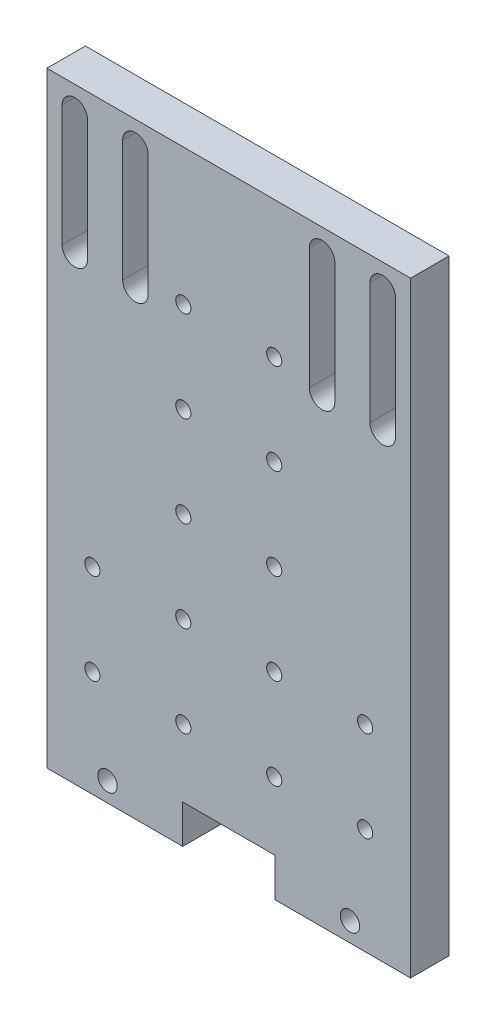
SolidWorks part; units mm, degrees
ref_plane "Front" through (0, 0, 0) normal (0, 0, 1) x (1, 0, 0)
ref_plane "Top" through (0, 0, 0) normal (0, 1, 0) x (1, 0, 0)
ref_plane "Right" through (0, 0, 0) normal (1, 0, 0) x (0, 0, -1)
ref_plane "Plane1" through (0, 0, 118.2886) normal (0, 0, 1) x (1, 0, 0)
sketch "Sketch1" plane through (0, 0, 118.2886) normal (0, 0, 1) x (1, 0, 0)
  line L0 (19.6347, 102.189) -> (19.6347, 2.189)
  line L1 (19.6347, 2.189) -> (42.0347, 2.189)
  line L2 (42.0347, 2.189) -> (42.0347, 8.539)
  line L3 (42.0347, 8.539) -> (57.2347, 8.539)
  line L4 (57.2347, 8.539) -> (57.2347, 2.189)
  line L5 (57.2347, 2.189) -> (79.6347, 2.189)
  line L6 (79.6347, 2.189) -> (79.6347, 102.189)
  line L7 (79.6347, 102.189) -> (19.6347, 102.189)
  dimension "D1" = 15.2
  dimension "D2" = 6.35
  dimension "D3" = 60
  dimension "D4" = 100
extrude "Boss-Extrude1" add sketch "Sketch1" against normal blind 6.35
hole_wizard "Ø2.5 (2.5) Diameter Hole1" positions "Sketch7" profile "Sketch6" hole size "Ø2.5" standard "ANSI Metric"
sketch "Sketch7" plane through (0, 0, 111.9386) normal (0, 0, -1) x (-1, 0, 0)
  point P0 (-27.1347, 19.689)
sketch "Sketch6" plane through (27.1347, 19.689, 111.9386) normal (1, 0, 0) x (0, 1, 0)
  line L0 (0, 0) -> (0, 6.35)
  line L1 (0, 6.35) -> (1.25, 6.35)
  line L2 (1.25, 6.35) -> (1.25, 0)
  line L5 (1.25, 0) -> (0, 0)
  line L11 (0, -6.35) -> (0, 107.95) construction
  dimension "Thru Hole Dia." = 2.5
  dimension "Thru Hole Depth" = 6.35
hole_wizard "Ø3.2 (3.2) Diameter Hole1" positions "Sketch9" profile "Sketch8" hole size "Ø3.2" standard "ANSI Metric"
sketch "Sketch9" plane through (0, 0, 118.2886) normal (0, 0, 1) x (1, 0, 0)
  point P0 (29.6347, 5.364)
sketch "Sketch8" plane through (29.6347, 5.364, 118.2886) normal (1, 0, 0) x (0, -1, 0)
  line L0 (0, 0) -> (0, 6.35)
  line L1 (0, 6.35) -> (1.6, 6.35)
  line L2 (1.6, 6.35) -> (1.6, 0)
  line L5 (1.6, 0) -> (0, 0)
  line L11 (0, -6.35) -> (0, 107.95) construction
  dimension "Thru Hole Dia." = 3.2
  dimension "Thru Hole Depth" = 6.35
hole_wizard "Ø2.5 (2.5) Diameter Hole2" positions "Sketch11" profile "Sketch10" hole size "Ø2.5" standard "ANSI Metric"
sketch "Sketch11" plane through (0, 0, 111.9386) normal (0, 0, -1) x (-1, 0, 0)
  point P0 (-57.1347, 19.689)
sketch "Sketch10" plane through (57.1347, 19.689, 111.9386) normal (1, 0, 0) x (0, 1, 0)
  line L0 (0, 0) -> (0, 6.35)
  line L1 (0, 6.35) -> (1.25, 6.35)
  line L2 (1.25, 6.35) -> (1.25, 0)
  line L5 (1.25, 0) -> (0, 0)
  line L11 (0, -6.35) -> (0, 107.95) construction
  dimension "Thru Hole Dia." = 2.5
  dimension "Thru Hole Depth" = 6.35
hole_wizard "Ø2.5 (2.5) Diameter Hole3" positions "Sketch13" profile "Sketch12" hole size "Ø2.5" standard "ANSI Metric"
sketch "Sketch13" plane through (0, 0, 111.9386) normal (0, 0, -1) x (-1, 0, 0)
  point P0 (-42.1347, 34.689)
sketch "Sketch12" plane through (42.1347, 34.689, 111.9386) normal (1, 0, 0) x (0, 1, 0)
  line L0 (0, 0) -> (0, 6.35)
  line L1 (0, 6.35) -> (1.25, 6.35)
  line L2 (1.25, 6.35) -> (1.25, 0)
  line L5 (1.25, 0) -> (0, 0)
  line L11 (0, -6.35) -> (0, 107.95) construction
  dimension "Thru Hole Dia." = 2.5
  dimension "Thru Hole Depth" = 6.35
hole_wizard "Ø2.5 (2.5) Diameter Hole4" positions "Sketch15" profile "Sketch14" hole size "Ø2.5" standard "ANSI Metric"
sketch "Sketch15" plane through (0, 0, 111.9386) normal (0, 0, -1) x (-1, 0, 0)
  point P0 (-42.1347, 64.689)
sketch "Sketch14" plane through (42.1347, 64.689, 111.9386) normal (1, 0, 0) x (0, 1, 0)
  line L0 (0, 0) -> (0, 6.35)
  line L1 (0, 6.35) -> (1.25, 6.35)
  line L2 (1.25, 6.35) -> (1.25, 0)
  line L5 (1.25, 0) -> (0, 0)
  line L11 (0, -6.35) -> (0, 107.95) construction
  dimension "Thru Hole Dia." = 2.5
  dimension "Thru Hole Depth" = 6.35
hole_wizard "Ø2.5 (2.5) Diameter Hole5" positions "Sketch17" profile "Sketch16" hole size "Ø2.5" standard "ANSI Metric"
sketch "Sketch17" plane through (0, 0, 111.9386) normal (0, 0, -1) x (-1, 0, 0)
  point P0 (-57.1347, 64.689)
sketch "Sketch16" plane through (57.1347, 64.689, 111.9386) normal (1, 0, 0) x (0, 1, 0)
  line L0 (0, 0) -> (0, 6.35)
  line L1 (0, 6.35) -> (1.25, 6.35)
  line L2 (1.25, 6.35) -> (1.25, 0)
  line L5 (1.25, 0) -> (0, 0)
  line L11 (0, -6.35) -> (0, 107.95) construction
  dimension "Thru Hole Dia." = 2.5
  dimension "Thru Hole Depth" = 6.35
hole_wizard "Ø2.5 (2.5) Diameter Hole6" positions "Sketch19" profile "Sketch18" hole size "Ø2.5" standard "ANSI Metric"
sketch "Sketch19" plane through (0, 0, 111.9386) normal (0, 0, -1) x (-1, 0, 0)
  point P0 (-27.1347, 34.689)
sketch "Sketch18" plane through (27.1347, 34.689, 111.9386) normal (1, 0, 0) x (0, 1, 0)
  line L0 (0, 0) -> (0, 6.35)
  line L1 (0, 6.35) -> (1.25, 6.35)
  line L2 (1.25, 6.35) -> (1.25, 0)
  line L5 (1.25, 0) -> (0, 0)
  line L11 (0, -6.35) -> (0, 107.95) construction
  dimension "Thru Hole Dia." = 2.5
  dimension "Thru Hole Depth" = 6.35
hole_wizard "Ø2.5 (2.5) Diameter Hole7" positions "Sketch21" profile "Sketch20" hole size "Ø2.5" standard "ANSI Metric"
sketch "Sketch21" plane through (0, 0, 111.9386) normal (0, 0, -1) x (-1, 0, 0)
  point P0 (-72.1347, 19.689)
sketch "Sketch20" plane through (72.1347, 19.689, 111.9386) normal (1, 0, 0) x (0, 1, 0)
  line L0 (0, 0) -> (0, 6.35)
  line L1 (0, 6.35) -> (1.25, 6.35)
  line L2 (1.25, 6.35) -> (1.25, 0)
  line L5 (1.25, 0) -> (0, 0)
  line L11 (0, -6.35) -> (0, 107.95) construction
  dimension "Thru Hole Dia." = 2.5
  dimension "Thru Hole Depth" = 6.35
hole_wizard "Ø2.5 (2.5) Diameter Hole8" positions "Sketch23" profile "Sketch22" hole size "Ø2.5" standard "ANSI Metric"
sketch "Sketch23" plane through (0, 0, 111.9386) normal (0, 0, -1) x (-1, 0, 0)
  point P0 (-42.1347, 19.689)
sketch "Sketch22" plane through (42.1347, 19.689, 111.9386) normal (1, 0, 0) x (0, 1, 0)
  line L0 (0, 0) -> (0, 6.35)
  line L1 (0, 6.35) -> (1.25, 6.35)
  line L2 (1.25, 6.35) -> (1.25, 0)
  line L5 (1.25, 0) -> (0, 0)
  line L11 (0, -6.35) -> (0, 107.95) construction
  dimension "Thru Hole Dia." = 2.5
  dimension "Thru Hole Depth" = 6.35
hole_wizard "Ø2.5 (2.5) Diameter Hole9" positions "Sketch25" profile "Sketch24" hole size "Ø2.5" standard "ANSI Metric"
sketch "Sketch25" plane through (0, 0, 111.9386) normal (0, 0, -1) x (-1, 0, 0)
  point P0 (-57.1347, 34.689)
sketch "Sketch24" plane through (57.1347, 34.689, 111.9386) normal (1, 0, 0) x (0, 1, 0)
  line L0 (0, 0) -> (0, 6.35)
  line L1 (0, 6.35) -> (1.25, 6.35)
  line L2 (1.25, 6.35) -> (1.25, 0)
  line L5 (1.25, 0) -> (0, 0)
  line L11 (0, -6.35) -> (0, 107.95) construction
  dimension "Thru Hole Dia." = 2.5
  dimension "Thru Hole Depth" = 6.35
hole_wizard "Ø2.5 (2.5) Diameter Hole10" positions "Sketch27" profile "Sketch26" hole size "Ø2.5" standard "ANSI Metric"
sketch "Sketch27" plane through (0, 0, 111.9386) normal (0, 0, -1) x (-1, 0, 0)
  point P0 (-42.1347, 49.689)
sketch "Sketch26" plane through (42.1347, 49.689, 111.9386) normal (1, 0, 0) x (0, 1, 0)
  line L0 (0, 0) -> (0, 6.35)
  line L1 (0, 6.35) -> (1.25, 6.35)
  line L2 (1.25, 6.35) -> (1.25, 0)
  line L5 (1.25, 0) -> (0, 0)
  line L11 (0, -6.35) -> (0, 107.95) construction
  dimension "Thru Hole Dia." = 2.5
  dimension "Thru Hole Depth" = 6.35
hole_wizard "Ø2.5 (2.5) Diameter Hole11" positions "Sketch29" profile "Sketch28" hole size "Ø2.5" standard "ANSI Metric"
sketch "Sketch29" plane through (0, 0, 111.9386) normal (0, 0, -1) x (-1, 0, 0)
  point P0 (-42.1347, 79.689)
sketch "Sketch28" plane through (42.1347, 79.689, 111.9386) normal (1, 0, 0) x (0, 1, 0)
  line L0 (0, 0) -> (0, 6.35)
  line L1 (0, 6.35) -> (1.25, 6.35)
  line L2 (1.25, 6.35) -> (1.25, 0)
  line L5 (1.25, 0) -> (0, 0)
  line L11 (0, -6.35) -> (0, 107.95) construction
  dimension "Thru Hole Dia." = 2.5
  dimension "Thru Hole Depth" = 6.35
hole_wizard "Ø2.5 (2.5) Diameter Hole12" positions "Sketch31" profile "Sketch30" hole size "Ø2.5" standard "ANSI Metric"
sketch "Sketch31" plane through (0, 0, 111.9386) normal (0, 0, -1) x (-1, 0, 0)
  point P0 (-57.1347, 79.689)
sketch "Sketch30" plane through (57.1347, 79.689, 111.9386) normal (1, 0, 0) x (0, 1, 0)
  line L0 (0, 0) -> (0, 6.35)
  line L1 (0, 6.35) -> (1.25, 6.35)
  line L2 (1.25, 6.35) -> (1.25, 0)
  line L5 (1.25, 0) -> (0, 0)
  line L11 (0, -6.35) -> (0, 107.95) construction
  dimension "Thru Hole Dia." = 2.5
  dimension "Thru Hole Depth" = 6.35
hole_wizard "Ø2.5 (2.5) Diameter Hole13" positions "Sketch33" profile "Sketch32" hole size "Ø2.5" standard "ANSI Metric"
sketch "Sketch33" plane through (0, 0, 111.9386) normal (0, 0, -1) x (-1, 0, 0)
  point P0 (-57.1347, 49.689)
sketch "Sketch32" plane through (57.1347, 49.689, 111.9386) normal (1, 0, 0) x (0, 1, 0)
  line L0 (0, 0) -> (0, 6.35)
  line L1 (0, 6.35) -> (1.25, 6.35)
  line L2 (1.25, 6.35) -> (1.25, 0)
  line L5 (1.25, 0) -> (0, 0)
  line L11 (0, -6.35) -> (0, 107.95) construction
  dimension "Thru Hole Dia." = 2.5
  dimension "Thru Hole Depth" = 6.35
hole_wizard "Ø2.5 (2.5) Diameter Hole14" positions "Sketch35" profile "Sketch34" hole size "Ø2.5" standard "ANSI Metric"
sketch "Sketch35" plane through (0, 0, 111.9386) normal (0, 0, -1) x (-1, 0, 0)
  point P0 (-72.1347, 34.689)
sketch "Sketch34" plane through (72.1347, 34.689, 111.9386) normal (1, 0, 0) x (0, 1, 0)
  line L0 (0, 0) -> (0, 6.35)
  line L1 (0, 6.35) -> (1.25, 6.35)
  line L2 (1.25, 6.35) -> (1.25, 0)
  line L5 (1.25, 0) -> (0, 0)
  line L11 (0, -6.35) -> (0, 107.95) construction
  dimension "Thru Hole Dia." = 2.5
  dimension "Thru Hole Depth" = 6.35
hole_wizard "Ø3.2 (3.2) Diameter Hole2" positions "Sketch37" profile "Sketch36" hole size "Ø3.2" standard "ANSI Metric"
sketch "Sketch37" plane through (0, 0, 118.2886) normal (0, 0, 1) x (1, 0, 0)
  point P0 (69.6347, 5.364)
sketch "Sketch36" plane through (69.6347, 5.364, 118.2886) normal (1, 0, 0) x (0, -1, 0)
  line L0 (0, 0) -> (0, 6.35)
  line L1 (0, 6.35) -> (1.6, 6.35)
  line L2 (1.6, 6.35) -> (1.6, 0)
  line L5 (1.6, 0) -> (0, 0)
  line L11 (0, -6.35) -> (0, 107.95) construction
  dimension "Thru Hole Dia." = 3.2
  dimension "Thru Hole Depth" = 6.35
sketch "Sketch38" plane through (0, 0, 118.2886) normal (0, 0, 1) x (1, 0, 0)
  line L0 (24.2347, 98.189) -> (24.2347, 78.189) construction
  line L1 (34.2347, 98.189) -> (34.2347, 78.189) construction
  line L3 (65.0347, 98.189) -> (65.0347, 78.189) construction
  line L4 (75.0347, 98.189) -> (75.0347, 78.189) construction
  line L5 (24.2347, 98.189) -> (75.0347, 98.189) construction
  line L6 (75.0347, 78.189) -> (24.2347, 78.189) construction
  line L7 (19.6347, 102.189) -> (19.6347, 2.189) construction
  line L8 (79.6347, 2.189) -> (79.6347, 102.189) construction
  line L9 (79.6347, 102.189) -> (19.6347, 102.189) construction
  line L10 (22.1347, 98.189) -> (22.1347, 78.189)
  line L11 (32.1347, 98.189) -> (32.1347, 78.189)
  line L12 (62.9347, 98.189) -> (62.9347, 78.189)
  line L13 (72.9347, 98.189) -> (72.9347, 78.189)
  line L14 (26.3347, 98.189) -> (26.3347, 78.189)
  line L15 (36.3347, 98.189) -> (36.3347, 78.189)
  line L16 (67.1347, 98.189) -> (67.1347, 78.189)
  line L17 (77.1347, 98.189) -> (77.1347, 78.189)
  arc A0 (22.1347, 98.189) -> (26.3347, 98.189) centre (24.2347, 98.189) cw
  arc A1 (22.1347, 78.189) -> (26.3347, 78.189) centre (24.2347, 78.189) ccw
  arc A2 (32.1347, 98.189) -> (36.3347, 98.189) centre (34.2347, 98.189) cw
  arc A3 (32.1347, 78.189) -> (36.3347, 78.189) centre (34.2347, 78.189) ccw
  arc A4 (62.9347, 98.189) -> (67.1347, 98.189) centre (65.0347, 98.189) cw
  arc A5 (62.9347, 78.189) -> (67.1347, 78.189) centre (65.0347, 78.189) ccw
  arc A6 (72.9347, 98.189) -> (77.1347, 98.189) centre (75.0347, 98.189) cw
  arc A7 (72.9347, 78.189) -> (77.1347, 78.189) centre (75.0347, 78.189) ccw
  dimension "D1" = 10
  dimension "D2" = 10
  dimension "D3" = 4.6
  dimension "D4" = 4.6
  dimension "D5" = 4
  dimension "D6" = 20
  dimension "D7" = 2.1
  dimension "D8" = 2.1
extrude "Cut-Extrude1" cut sketch "Sketch38" against normal through all
